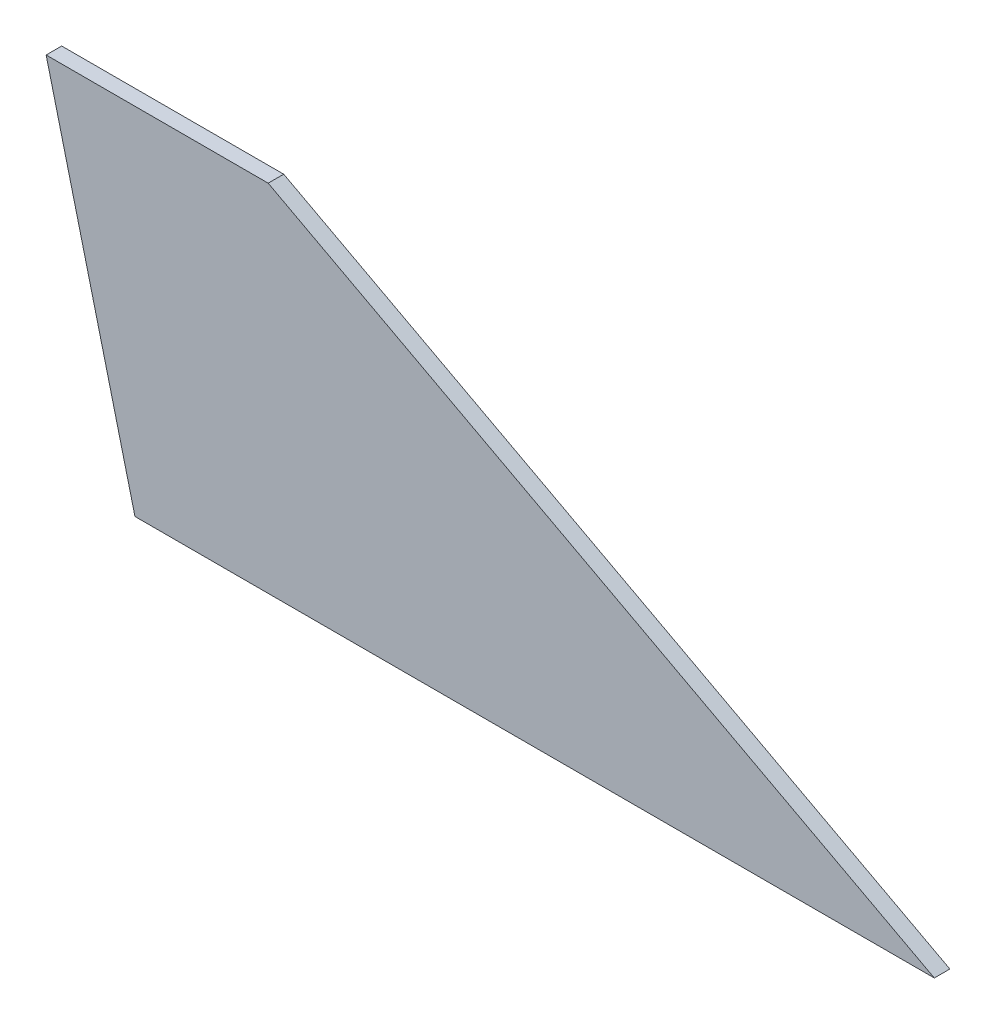
SolidWorks part; units mm, degrees
ref_plane "Front Plane" through (0, 0, 0) normal (0, 0, 1) x (1, 0, 0)
ref_plane "Top Plane" through (0, 0, 0) normal (0, 1, 0) x (1, 0, 0)
ref_plane "Right Plane" through (0, 0, 0) normal (1, 0, 0) x (0, 0, -1)
sketch "Sketch1" plane through (0, 0, 0) normal (0, 0, 1) x (1, 0, 0)
  line L0 (0, 0) -> (457.2, 0)
  line L1 (457.2, 0) -> (76.2, 203.2)
  line L2 (76.2, 203.2) -> (-50.8, 203.2)
  line L3 (-50.8, 203.2) -> (0, 0)
  dimension "D1" = 457.2
  dimension "D2" = 203.2
  dimension "D3" = 127
  dimension "D4" = 381
extrude "Boss-Extrude1" add sketch "Sketch1" along normal blind 8.89
